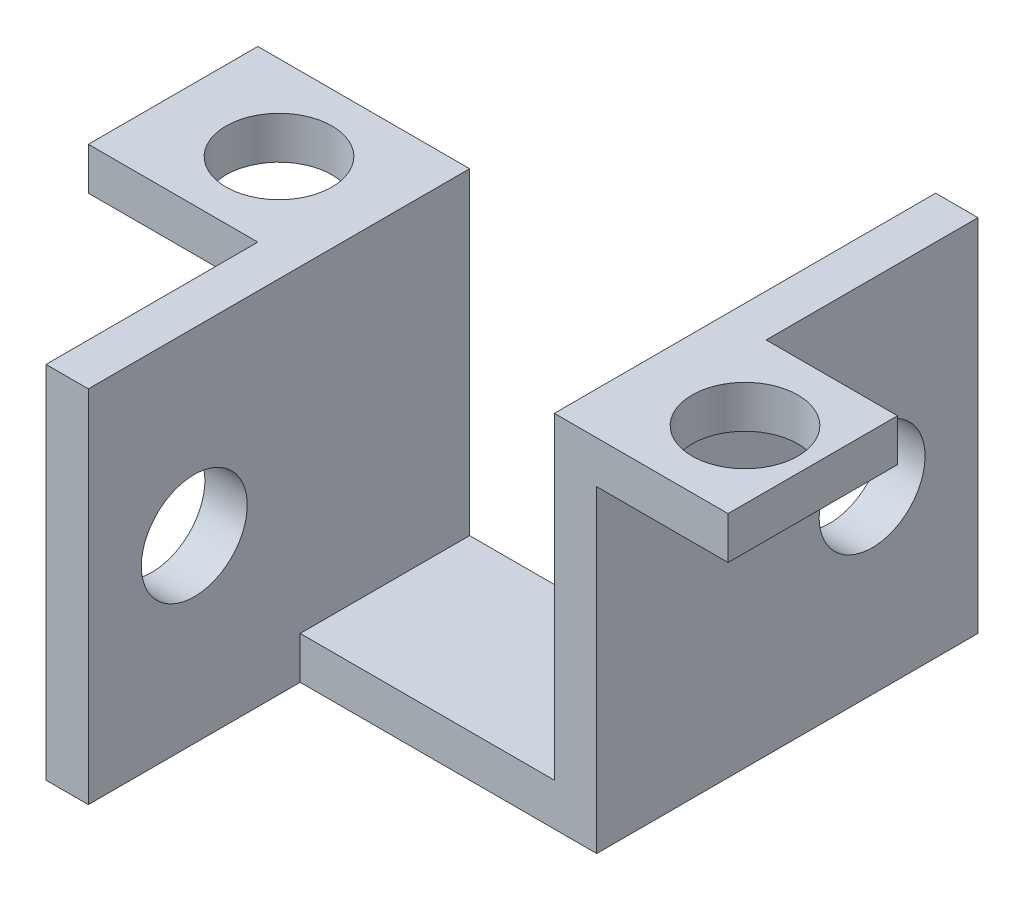
SolidWorks part; units mm, degrees
ref_plane "Alzado" through (0, 0, 0) normal (0, 0, 1) x (1, 0, 0)
ref_plane "Planta" through (0, 0, 0) normal (0, 1, 0) x (1, 0, 0)
ref_plane "Vista lateral" through (0, 0, 0) normal (1, 0, 0) x (0, 0, -1)
sketch "Croquis1" plane through (0, 0, 0) normal (0, 0, 1) x (1, 0, 0)
  line L0 (-6, 7.5) -> (-8, 7.5)
  line L1 (-6, -7.5) -> (6, -7.5)
  line L2 (-6, -7.5) -> (-6, 7.5)
  line L4 (6, -7.5) -> (6, 7.5)
  line L5 (-6, -7.5) -> (6, 7.5) construction
  line L6 (-6, 7.5) -> (6, -7.5) construction
  line L7 (8, 7.5) -> (6, 7.5)
  line L8 (8, 5.5) -> (8, -9.5)
  line L9 (8, -9.5) -> (-8, -9.5)
  line L10 (-8, 5.5) -> (-8, -9.5)
  line L11 (8, 7.5) -> (16, 7.5)
  line L12 (8, 7.5) -> (8, 5.5)
  line L13 (8, 5.5) -> (16, 5.5)
  line L14 (16, 7.5) -> (16, 5.5)
  line L15 (-8, 7.5) -> (-16, 7.5)
  line L16 (-8, 7.5) -> (-8, 5.5)
  line L17 (-8, 5.5) -> (-16, 5.5)
  line L18 (-16, 7.5) -> (-16, 5.5)
  point P0 (0, 0)
  dimension "D1" = 12
  dimension "D2" = 15
  dimension "D3" = 2
  dimension "D4" = 2
  dimension "D5" = 17
  dimension "D6" = 8
  dimension "D7" = 2
  dimension "D8" = 2
  dimension "D9" = 8
extrude "Saliente-Extruir1" add sketch "Croquis1" along normal blind 8 contours L15 L18 L17 L16 | L0 L16 L10 L9 L8 L12 L7 L4 L1 L2 | L14 L11 L12 L13
sketch "Croquis2" plane through (0, 7.5, 0) normal (0, 1, 0) x (1, 0, 0)
  line L0 (-16, -4) -> (-11, -4) construction
  line L1 (-16, -8) -> (-16, 0) construction
  line L2 (-11, 0) -> (-11, -4) construction
  line L3 (-6, 0) -> (-16, 0) construction
  line L4 (16, -4) -> (11, -4) construction
  line L5 (16, -8) -> (16, 0) construction
  line L6 (11, 0) -> (11, -4) construction
  line L7 (16, 0) -> (6, 0) construction
  circle A0 centre (-11, -4) radius 2.5
  circle A1 centre (11, -4) radius 2.5
  dimension "D1" = 5
  dimension "D2" = 5
extrude "Cortar-Extruir1" cut sketch "Croquis2" against normal blind 2
sketch "Sketch1" plane through (16, 0, 0) normal (1, 0, 0) x (0, 0, -1)
  line L1 (-8, 7.5) -> (0, 7.5)
  line L2 (-8, 7.5) -> (-8, 5.5)
  line L3 (-8, 5.5) -> (0, 5.5)
  line L4 (0, 7.5) -> (0, 5.5)
extrude "Cut-Extrude1" cut sketch "Sketch1" against normal blind 1.8
sketch "Sketch5" plane through (-8, 0, 0) normal (-1, 0, 0) x (0, 0, 1)
  line L1 (8, -9.5) -> (18, -9.5)
  line L2 (8, -9.5) -> (8, 7.5)
  line L3 (8, 7.5) -> (18, 7.5)
  line L4 (18, -9.5) -> (18, 7.5)
  circle A0 centre (13, -1) radius 2.5
  point P7 (13, -1)
  point P9 (16.7971, -1.8583)
  dimension "D3" = 5
  dimension "D1" = 17
  dimension "D2" = 10
  dimension "D4" = 5
  dimension "D5" = 8.5
extrude "Boss-Extrude3" add sketch "Sketch5" against normal blind 2 contours L2 L1 L4 L3
sketch "Sketch6" plane through (8, 0, 0) normal (1, 0, 0) x (0, 0, -1)
  line L1 (0, -9.5) -> (10, -9.5)
  line L2 (0, -9.5) -> (0, 7.5)
  line L3 (0, 7.5) -> (10, 7.5)
  line L4 (10, -9.5) -> (10, 7.5)
  circle A0 centre (5, -1) radius 2.5
  dimension "D3" = 5
  dimension "D1" = 17
  dimension "D2" = 10
  dimension "D4" = 5
  dimension "D5" = 8.5
extrude "Boss-Extrude4" add sketch "Sketch6" against normal blind 2
sketch "Sketch7" plane through (-8, 0, 0) normal (-1, 0, 0) x (0, 0, 1)
  line L0 (18, -9.5) -> (18, 7.5) construction
  line L1 (18, -9.5) -> (0, -9.5) construction
  circle A0 centre (13, -1) radius 2.5
  dimension "D1" = 5
  dimension "D2" = 5
  dimension "D3" = 8.5
extrude "Cut-Extrude2" cut sketch "Sketch7" against normal blind 2
